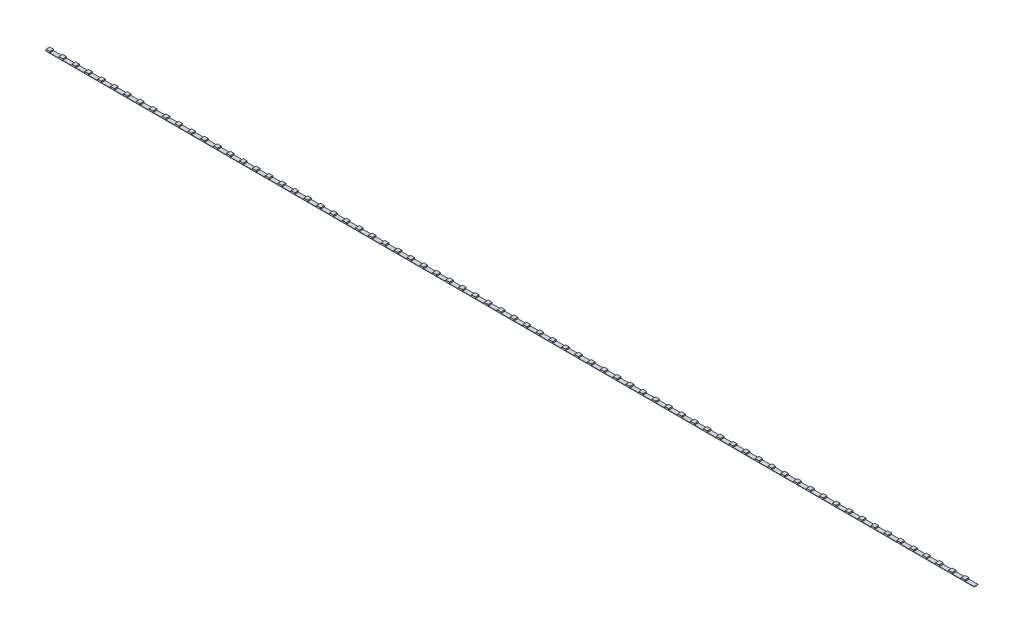
SolidWorks part; units mm, degrees
material "6061-T6 (SS)"
ref_plane "前视基准面" through (0, 0, 0) normal (0, 0, 1) x (1, 0, 0)
ref_plane "上视基准面" through (0, 0, 0) normal (0, 1, 0) x (1, 0, 0)
ref_plane "右视基准面" through (0, 0, 0) normal (1, 0, 0) x (0, 0, -1)
sketch "草图1" plane through (0, 0, 0) normal (0, 1, 0) x (1, 0, 0)
  line L1 (-600, 2.5) -> (600, 2.5)
  line L2 (-600, 2.5) -> (-600, -2.5)
  line L3 (-600, -2.5) -> (600, -2.5)
  line L4 (600, 2.5) -> (600, -2.5)
  line L5 (-600, 2.5) -> (600, -2.5) construction
  line L6 (-600, -2.5) -> (600, 2.5) construction
  point P0 (0, 0)
  dimension "D1" = 5
  dimension "D2" = 1200
extrude "凸台-拉伸1" add sketch "草图1" along normal blind 0.5
sketch "草图2" plane through (0, 0.5, 0) normal (0, 1, 0) x (1, 0, 0)
  line L0 (600, 2.5) -> (-600, 2.5) construction
  line L1 (-600, -2.5) -> (-595, -2.5)
  line L2 (-600, -2.5) -> (-600, 2.5)
  line L3 (-600, 2.5) -> (-595, 2.5)
  line L4 (-595, -2.5) -> (-595, 2.5)
  dimension "D1" = 5
extrude "凸台-拉伸2" add sketch "草图2" along normal blind 1.7
pattern_linear "阵列(线性)1" count 72 spacing 16.6667 along (1, 0, 0) of "凸台-拉伸2"
